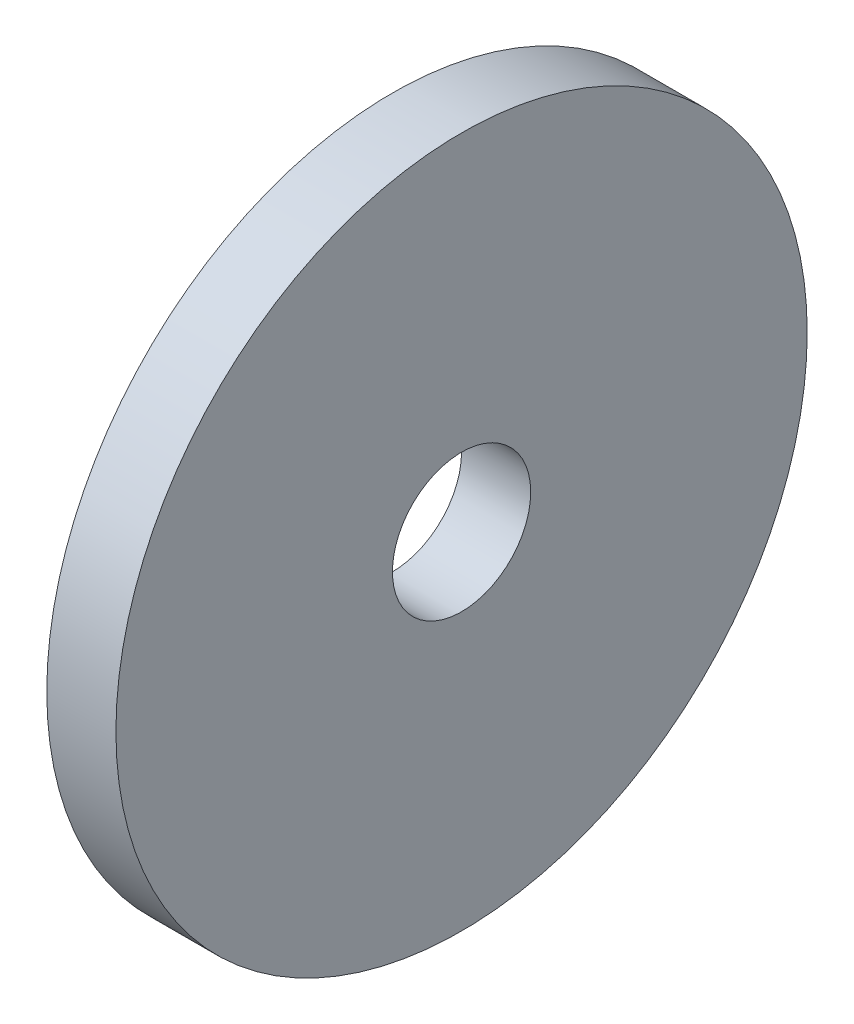
SolidWorks part; units mm, degrees
ref_plane "Front Plane" through (0, 0, 0) normal (0, 0, 1) x (1, 0, 0)
ref_plane "Top Plane" through (0, 0, 0) normal (0, 1, 0) x (1, 0, 0)
ref_plane "Right Plane" through (0, 0, 0) normal (1, 0, 0) x (0, 0, -1)
sketch "Sketch1" plane through (0, 0, 0) normal (1, 0, 0) x (0, 0, -1)
  circle A0 centre (0, 0) radius 50
  circle A1 centre (0, 0) radius 10
  dimension "D1" = 100
  dimension "D2" = 20
extrude "Boss-Extrude1" add sketch "Sketch1" along normal blind 10
